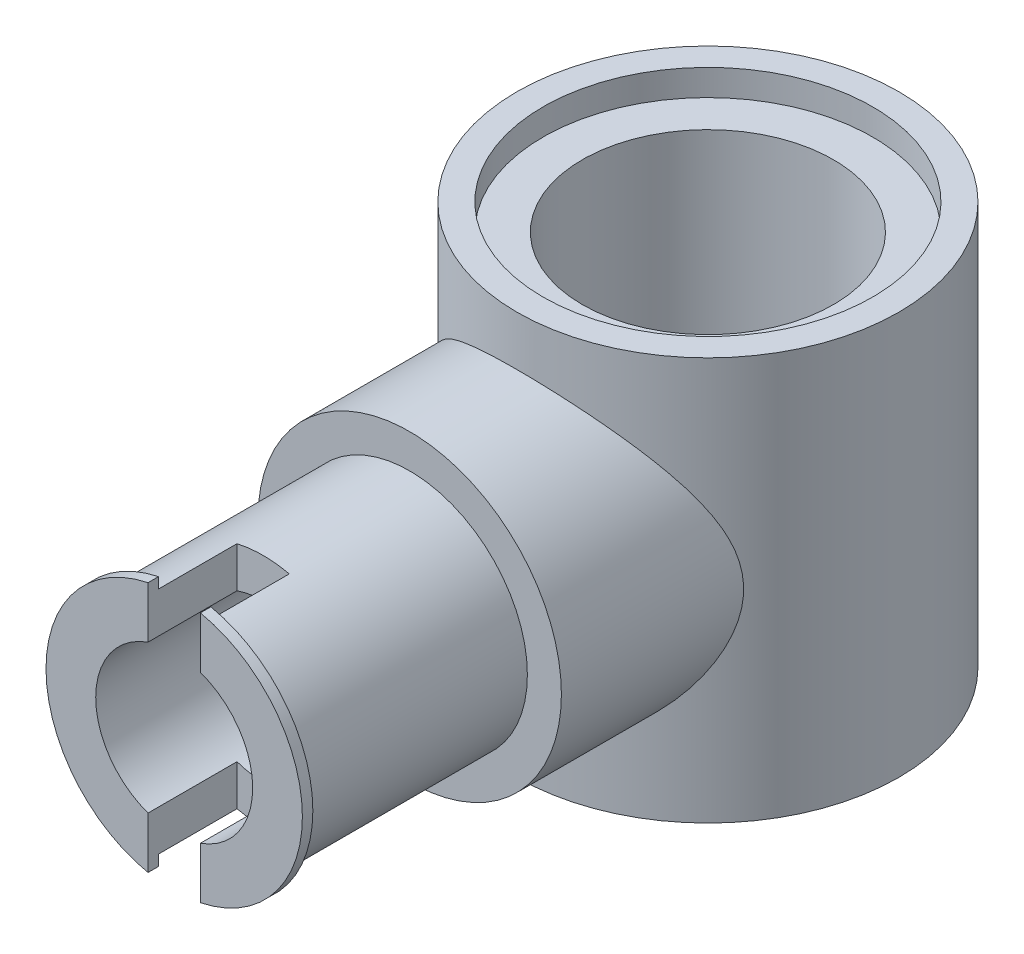
SolidWorks part; units mm, degrees
ref_plane "Front Plane" through (0, 0, 0) normal (0, 0, 1) x (1, 0, 0)
ref_plane "Top Plane" through (0, 0, 0) normal (0, 1, 0) x (1, 0, 0)
ref_plane "Right Plane" through (0, 0, 0) normal (1, 0, 0) x (0, 0, -1)
sketch "Sketch1" plane through (0, 0, 0) normal (0, 1, 0) x (1, 0, 0)
  circle A0 centre (0, 0) radius 3.65
  circle A1 centre (0, 0) radius 2.4
extrude "Boss-Extrude1" add sketch "Sketch1" along normal blind 7.7
sketch "Sketch2" plane through (0, 7.7, 0) normal (0, 1, 0) x (1, 0, 0)
  circle A0 centre (0, 0) radius 2.4
  circle A1 centre (0, 0) radius 3.15
  circle A2 centre (0, 0) radius 3.65 construction
  circle M4 centre (0, 0) radius 2.4
  dimension "D1" = 0.5
extrude "Cut-Extrude1" cut sketch "Sketch2" against normal blind 0.5 contours A1 M4
ref_plane "Plane1" through (0, 3.85, 0) normal (0, 1, 0) x (1, 0, 0)
sketch "Sketch4" plane through (0, 0, 0) normal (0, 0, 1) x (1, 0, 0)
  line L0 (4.015, 3.85) -> (-4.015, 3.85) construction
  circle A0 centre (0, 3.85) radius 2.9
extrude "Boss-Extrude2" add sketch "Sketch4" along normal blind 5.7
sketch "Sketch5" plane through (0, 0, 0) normal (0, 0, 1) x (1, 0, 0)
  line L0 (4.015, 3.85) -> (-4.015, 3.85) construction
  circle A0 centre (0, 3.85) radius 2.25
  circle A1 centre (0, 3.85) radius 1.5 construction
extrude "Boss-Extrude3" add sketch "Sketch5" along normal blind 10.2
sketch "Sketch8" plane through (0, 7.2, 0) normal (0, 1, 0) x (1, 0, 0)
  circle A0 centre (0, 0) radius 2.4
extrude "Cut-Extrude5" cut sketch "Sketch8" against normal through all
ref_plane "Plane2" through (0, 0, 2.85) normal (0, 0, 1) x (1, 0, 0)
sketch "Sketch9" plane through (0, 0, 2.85) normal (0, 0, 1) x (1, 0, 0)
  circle A0 centre (0, 3.85) radius 2.25
ref_plane "Plane4" through (0, 0, 10) normal (0, 0, 1) x (1, 0, 0)
sketch "Sketch14" plane through (0, 0, 10) normal (0, 0, 1) x (1, 0, 0)
  circle A0 centre (0, 3.85) radius 2.25
  circle A1 centre (0, 3.85) radius 2.45
  dimension "D1" = 0.2
extrude "Boss-Extrude5" add sketch "Sketch14" along normal blind 0.2
sketch "Sketch10" plane through (0, 0, 2.85) normal (0, 0, 1) x (1, 0, 0)
  circle A0 centre (0, 3.85) radius 1.5
  dimension "D1" = 3
extrude "Cut-Extrude6" cut sketch "Sketch10" along normal through all contours A0
sketch "Sketch7" plane through (0, 0, 10.2) normal (0, 0, 1) x (1, 0, 0)
  line L0 (4.015, 3.85) -> (-4.015, 3.85) construction
  line L1 (0.5, 0.8607) -> (-0.5, 0.8607)
  line L2 (0.5, 0.8607) -> (0.5, 6.8393)
  line L3 (0.5, 6.8393) -> (-0.5, 6.8393)
  line L4 (-0.5, 0.8607) -> (-0.5, 6.8393)
  line L5 (0.5, 0.8607) -> (-0.5, 6.8393) construction
  line L6 (0.5, 6.8393) -> (-0.5, 0.8607) construction
  point P0 (0, 3.85)
  dimension "D1" = 1
extrude "Cut-Extrude7" cut sketch "Sketch7" against normal blind 1.7
